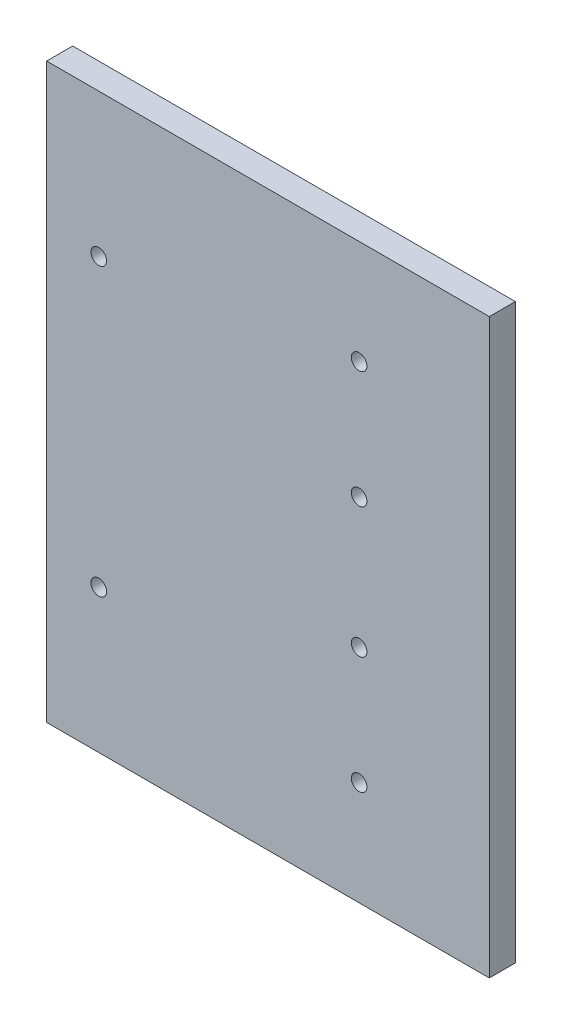
SolidWorks part; units mm, degrees
material "Polywood"
ref_plane "Front Plane" through (0, 0, 0) normal (0, 0, 1) x (1, 0, 0)
ref_plane "Top Plane" through (0, 0, 0) normal (0, 1, 0) x (1, 0, 0)
ref_plane "Right Plane" through (0, 0, 0) normal (1, 0, 0) x (0, 0, -1)
sketch "Sketch1" plane through (0, 0, 0) normal (0, 0, 1) x (1, 0, 0)
  line L1 (85, -55) -> (-85, -55)
  line L2 (85, -55) -> (85, 55)
  line L3 (85, 55) -> (-85, 55)
  line L4 (-85, -55) -> (-85, 55)
  line L5 (85, -55) -> (-85, 55) construction
  line L6 (85, 55) -> (-85, -55) construction
  point P0 (0, 0)
  dimension "D1" = 170
  dimension "D2" = 110
extrude "Boss-Extrude1" add sketch "Sketch1" along normal blind 5
sketch "Sketch2" plane through (0, 0, 5) normal (0, 0, 1) x (1, 0, 0)
  line L0 (-59.4334, 0) -> (49940.5666, 0) construction
  line L2 (-85, 55) -> (-85, -55) construction
  line L3 (0, 0) -> (0, -50000) construction
  circle A0 centre (-75, 27.5) radius 1.5
  circle A1 centre (-75, -27.5) radius 1.5
  circle A2 centre (75, -27.5) radius 1.5
  circle A3 centre (75, 27.5) radius 1.5
  dimension "D3" = 3
  dimension "D1" = 27.5
  dimension "D2" = 10
extrude "Cut-Extrude1" cut sketch "Sketch2" against normal through all
sketch "Sketch3" plane through (0, 0, 5) normal (0, 0, 1) x (1, 0, 0)
  line L0 (0, 0) -> (50000, 0) construction
  line L1 (0, 0) -> (0, -50000) construction
  line L2 (-21.1397, 23.75) -> (49978.8603, 23.75) construction
  line L3 (85, 55) -> (-85, 55) construction
  circle A0 centre (-25, 35) radius 1.5
  circle A1 centre (-25, 12.5) radius 1.5
  circle A2 centre (-25, -12.5) radius 1.5
  circle A3 centre (-25, -35) radius 1.5
  circle A4 centre (25, -35) radius 1.5
  circle A5 centre (25, -12.5) radius 1.5
  circle A6 centre (25, 12.5) radius 1.5
  circle A7 centre (25, 35) radius 1.5
  dimension "D2" = 3
  dimension "D3" = 20
  dimension "D1" = 25
  dimension "D4" = 11.25
extrude "Cut-Extrude2" cut sketch "Sketch3" against normal through all
sketch "Sketch4" plane through (0, 0, 0) normal (1, 0, 0) x (0, 0, -1)
  line L1 (14.9378, 59.0611) -> (-25.8515, 59.0611)
  line L2 (14.9378, 59.0611) -> (14.9378, -61.6389)
  line L3 (14.9378, -61.6389) -> (-25.8515, -61.6389)
  line L4 (-25.8515, 59.0611) -> (-25.8515, -61.6389)
extrude "Cut-Extrude3" cut sketch "Sketch4" along normal through all
